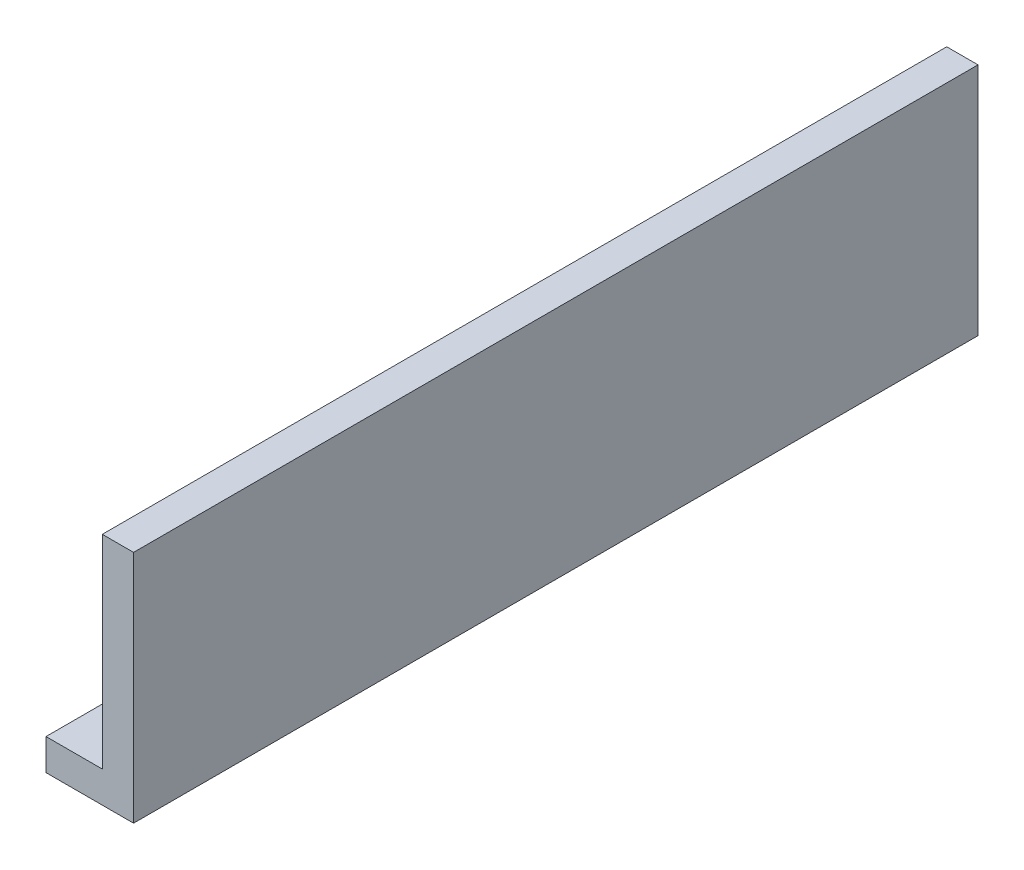
SolidWorks part; units mm, degrees
material "Malleable Cast Iron"
ref_plane "Front Plane" through (0, 0, 0) normal (0, 0, 1) x (1, 0, 0)
ref_plane "Top Plane" through (0, 0, 0) normal (0, 1, 0) x (1, 0, 0)
ref_plane "Right Plane" through (0, 0, 0) normal (1, 0, 0) x (0, 0, -1)
sketch "Sketch1" plane through (0, 0, 0) normal (0, 1, 0) x (1, 0, 0)
  line L1 (0, -270) -> (20, -270)
  line L2 (0, -270) -> (0, 270)
  line L3 (0, 270) -> (20, 270)
  line L4 (20, -270) -> (20, 270)
  dimension "D1" = 270
  dimension "D2" = 540
  dimension "D3" = 20
  dimension "D4" = 270
extrude "Boss-Extrude1" add sketch "Sketch1" along normal blind 150
sketch "Sketch2" plane through (0, 0, 0) normal (1, 0, 0) x (0, 0, -1)
  line L0 (-270, 150) -> (-270, 0) construction
  line L1 (-270, 20) -> (270, 20)
  line L2 (-270, 20) -> (-270, 0)
  line L3 (-270, 0) -> (270, 0)
  line L4 (270, 20) -> (270, 0)
  dimension "D1" = 20
extrude "Boss-Extrude2" add sketch "Sketch2" against normal blind 36
sketch "Sketch4" plane through (0, 20, 0) normal (0, 1, 0) x (1, 0, 0)
  point P0 (-16, 80)
  point P1 (-16, 160)
  point P2 (-16, 240)
  dimension "D1" = 80
  dimension "D2" = 80
  dimension "D3" = 80
  dimension "D4" = 16
hole_wizard "M10 Tapped Hole1" positions "Sketch5" profile "Sketch6" tap size "M10" standard "ISO"
sketch "Sketch5" plane through (0, 20, 0) normal (0, 1, 0) x (1, 0, 0)
  point P0 (-16, 80)
  point P3 (-16, 160)
  point P6 (-16, 240)
sketch "Sketch6" plane through (-16, 20, -80) normal (1, 0, 0) x (0, 0, 1)
  line L0 (0, 0) -> (0, 27.5)
  line L1 (0, 27.5) -> (4.25, 24.9463)
  line L2 (4.25, 24.9463) -> (4.25, 0.775)
  line L3 (4.25, 0.775) -> (5.025, 0)
  line L5 (5.025, 0) -> (0, 0)
  line L6 (-4.25, 0.775) -> (-5.025, 0) construction
  line L10 (0, 27.5) -> (-4.25, 24.9463) construction
  line L11 (0, -6.35) -> (0, 107.95) construction
  dimension "Tap Drill Dia." = 8.5
  dimension "Tap Drill Depth" = 27.5
  dimension "Near C'Sink Dia." = 10.05
  dimension "Near C'Sink Angle" = 90
  dimension "Drill Angle" = 118
cosmetic thread "Hole Thread1" parameters "D1"=20, "D2"=10
cosmetic thread "Hole Thread2" parameters "D1"=20, "D2"=10
cosmetic thread "Hole Thread3" parameters "D1"=20, "D2"=10
mirror "Mirror1" about plane through (0, 0, 0) normal (0, 0, 1) of "M10 Tapped Hole1"
cosmetic thread "Hole Thread4" parameters "D1"=20, "D2"=10
cosmetic thread "Hole Thread5" parameters "D1"=20, "D2"=10
cosmetic thread "Hole Thread6" parameters "D1"=20, "D2"=10
